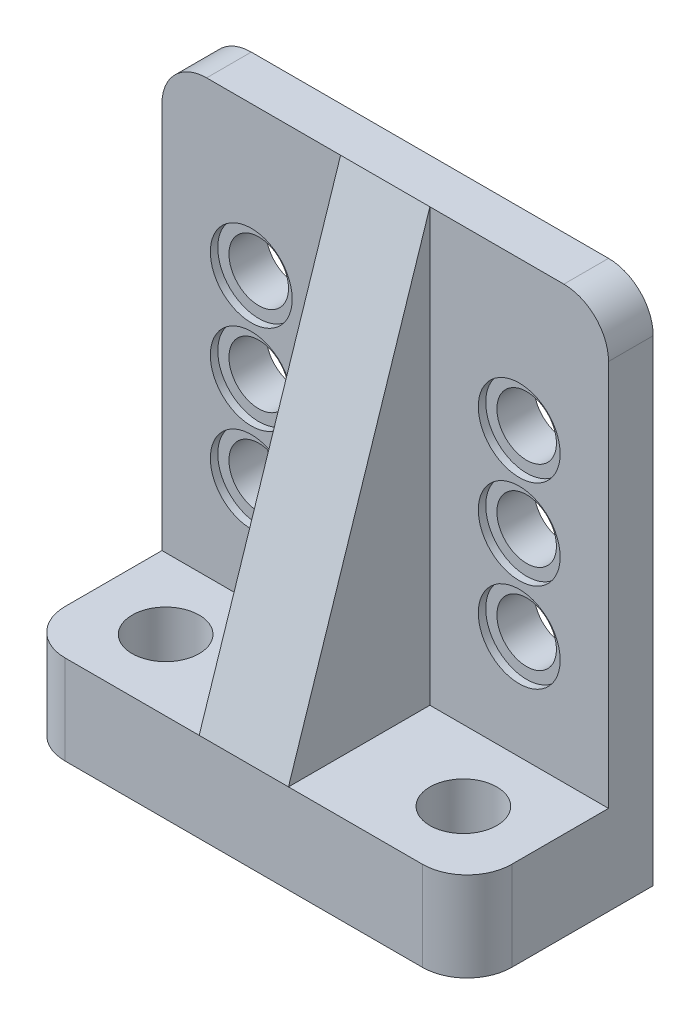
SolidWorks part; units mm, degrees
ref_plane "Front" through (0, 0, 0) normal (0, 0, 1) x (1, 0, 0)
ref_plane "Top" through (0, 0, 0) normal (0, 1, 0) x (1, 0, 0)
ref_plane "Right" through (0, 0, 0) normal (1, 0, 0) x (0, 0, -1)
sketch "Esquisse1" plane through (0, 0, 0) normal (0, 0, 1) x (1, 0, 0)
  line L1 (0, 0) -> (30, 0)
  line L2 (0, 0) -> (0, 35)
  line L3 (0, 35) -> (30, 35)
  line L4 (30, 0) -> (30, 35)
  dimension "D1" = 30
  dimension "D2" = 35
extrude "Boss.-Extru.1" add sketch "Esquisse1" along normal blind 3
sketch "Esquisse2" plane through (0, 0, 3) normal (0, 0, 1) x (1, 0, 0)
  line L0 (15, 0) -> (15, 25) construction
  line L1 (0, 0) -> (30, 0) construction
  line L2 (15, 25) -> (6, 25) construction
  line L3 (15, 19) -> (6, 19) construction
  line L4 (15, 13) -> (6, 13) construction
  line L5 (6, 19) -> (6, 25) construction
  circle A0 centre (6, 25) radius 2
  circle A1 centre (24, 25) radius 2
  circle A2 centre (24, 13) radius 2
  circle A3 centre (6, 13) radius 2
  circle A4 centre (6, 19) radius 2
  circle A5 centre (24, 19) radius 2
  dimension "D1" = 4
  dimension "D3" = 12
  dimension "D2" = 9
  dimension "D4" = 25
extrude "Enlèv. mat.-Extru.1" cut sketch "Esquisse2" against normal through all both and the other way through all
sketch "Esquisse3" plane through (0, 0, 3) normal (0, 0, 1) x (1, 0, 0)
  line L0 (30, 0) -> (30, 35) construction
  line L1 (0, 0) -> (30, 0)
  line L2 (0, 0) -> (0, 6)
  line L3 (0, 6) -> (30, 6)
  line L4 (30, 0) -> (30, 6)
  dimension "D1" = 6
extrude "Boss.-Extru.2" add sketch "Esquisse3" along normal blind 9.5
sketch "Esquisse4" plane through (0, 6, 0) normal (0, 1, 0) x (1, 0, 0)
  line L0 (30, -7.75) -> (15, -7.75) construction
  line L1 (30, -12.5) -> (30, -3) construction
  line L2 (15, -7.75) -> (15, -12.5) construction
  line L3 (30, -12.5) -> (0, -12.5) construction
  circle A0 centre (25, -7.75) radius 2.25
  circle A1 centre (5, -7.75) radius 2.25
  dimension "D1" = 20
  dimension "D2" = 4.5
extrude "Enlèv. mat.-Extru.2" cut sketch "Esquisse4" against normal through all both and the other way through all
sketch "Esquisse5" plane through (30, 0, 0) normal (1, 0, 0) x (0, 0, -1)
  line L0 (-12.5, 6) -> (-3, 35)
  line L1 (-3, 35) -> (-3, 6)
  line L2 (-3, 6) -> (-12.5, 6)
extrude "Boss.-Extru.3" add sketch "Esquisse5" along normal blind 6 from offset 18 offset against normal yes
fillet "Congé1" radius 3 4 edges at (0, 3, 12.5) (30, 3, 12.5) (30, 35, 1.5) (0, 35, 1.5)
sketch "Esquisse6" plane through (0, 0, 3) normal (0, 0, 1) x (1, 0, 0)
  circle A0 centre (24, 25) radius 2.75
  circle A1 centre (24, 19) radius 2.75
  circle A2 centre (24, 13) radius 2.75
  circle A3 centre (6, 13) radius 2.75
  circle A4 centre (6, 19) radius 2.75
  circle A5 centre (6, 25) radius 2.75
  dimension "D1" = 5.5
extrude "Enlèv. mat.-Extru.3" cut sketch "Esquisse6" against normal blind 0.5
